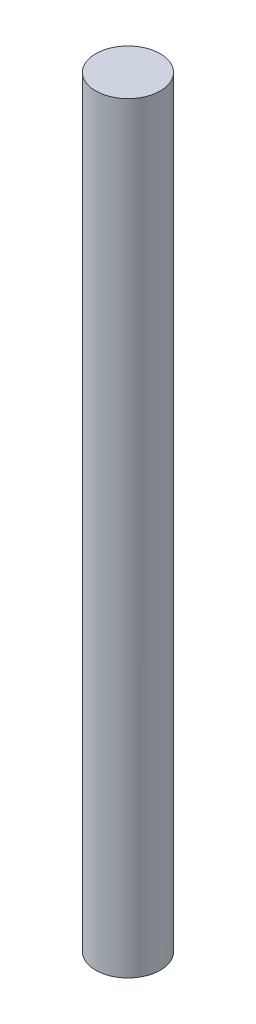
SolidWorks part; units mm, degrees
ref_plane "前视基准面" through (0, 0, 0) normal (0, 0, 1) x (1, 0, 0)
ref_plane "上视基准面" through (0, 0, 0) normal (0, 1, 0) x (1, 0, 0)
ref_plane "右视基准面" through (0, 0, 0) normal (1, 0, 0) x (0, 0, -1)
sketch "草图1" plane through (0, 2.8699, 0) normal (0, -1, 0) x (1, 0, 0)
  circle A0 centre (0, 0) radius 0.75
  dimension "D1" = 1.5
extrude "凸台-拉伸1" add sketch "草图1" along normal up to surface (17.7 mm away)
